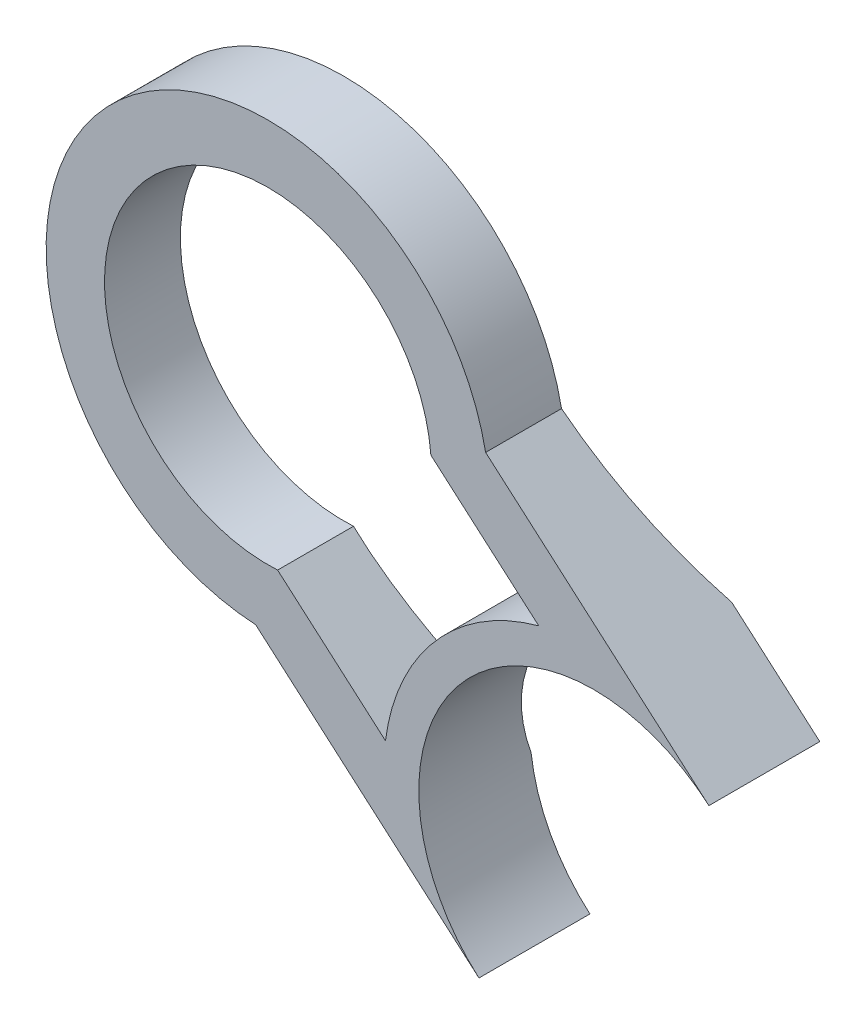
SolidWorks part; units mm, degrees
ref_plane "Front Plane" through (0, 0, 0) normal (0, 0, 1) x (1, 0, 0)
ref_plane "Top Plane" through (0, 0, 0) normal (0, 1, 0) x (1, 0, 0)
ref_plane "Right Plane" through (0, 0, 0) normal (1, 0, 0) x (0, 0, -1)
sketch "Sketch1" plane through (0, 0, 0) normal (0, 0, 1) x (1, 0, 0)
  line L0 (-265.158, 195.9991) -> (-226.9119, 162.7186)
  line L1 (-304.5442, 150.7362) -> (-266.2981, 117.4557)
  line L2 (-300.7921, 160.7272) -> (-282.3148, 144.6488)
  line L3 (-274.5346, 190.9024) -> (-256.0573, 174.8241)
  arc A0 (-265.158, 195.9991) -> (-304.5442, 150.7362) centre (-302.4461, 188.6783) ccw
  arc A1 (-226.9119, 162.7186) -> (-266.2981, 117.4557) centre (-246.605, 140.0872) ccw
  arc A2 (-274.5346, 190.9024) -> (-300.7921, 160.7272) centre (-302.4461, 188.6783) ccw
  arc A3 (-256.0573, 174.8241) -> (-282.3148, 144.6488) centre (-246.605, 140.0872) ccw
  dimension "D1" = 10
  dimension "D2" = 10
  dimension "D3" = 10
  dimension "D4" = 6
extrude "Boss-Extrude1" add sketch "Sketch1" along normal blind 19
sketch "Sketch2" plane through (-17.1997, -19.766, 0) normal (0.6564, 0.7544, 0) x (0.7544, -0.6564, 0)
  line L0 (-277.9925, 0) -> (-328.6911, 0) construction
  line L1 (-407.0264, 14.1421) -> (-297.9925, 14.1421)
  line L2 (-407.0264, 14.1421) -> (-407.0264, -6)
  line L3 (-407.0264, -6) -> (-328.7161, -6)
  line L4 (-297.9925, 14.1421) -> (-297.9925, 0)
  line L5 (-277.9925, -19) -> (-277.9925, 0) construction
  arc A0 (-297.9925, 0) -> (-328.7161, -6) centre (-332.2849, 93.9363) cw
  dimension "D3" = 100
  dimension "D1" = 6
  dimension "D2" = 20
extrude "Cut-Extrude1" cut sketch "Sketch2" against normal through all and the other way through all
